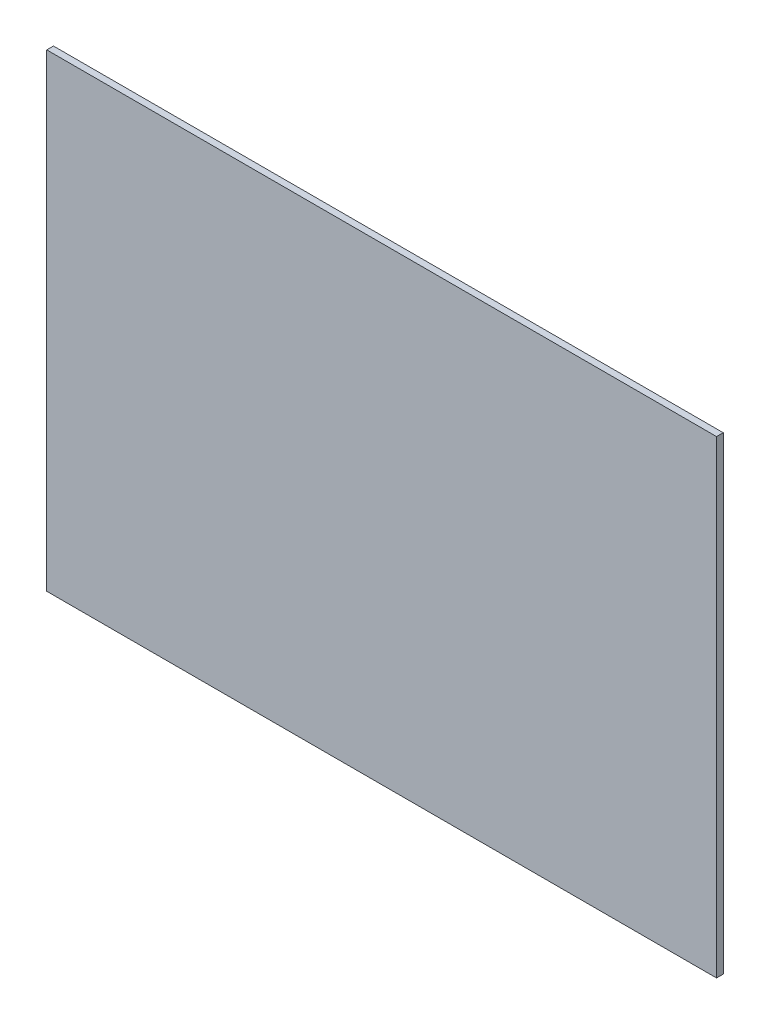
SolidWorks part; units mm, degrees
ref_plane "Alzado" through (0, 0, 0) normal (0, 0, 1) x (1, 0, 0)
ref_plane "Planta" through (0, 0, 0) normal (0, 1, 0) x (1, 0, 0)
ref_plane "Vista lateral" through (0, 0, 0) normal (1, 0, 0) x (0, 0, -1)
sketch "Croquis1" plane through (0, 0, 0) normal (0, 0, 1) x (1, 0, 0)
  line L1 (-62.4441, 24.485) -> (37.5559, 24.485)
  line L2 (-62.4441, 24.485) -> (-62.4441, -45.515)
  line L3 (-62.4441, -45.515) -> (37.5559, -45.515)
  line L4 (37.5559, 24.485) -> (37.5559, -45.515)
  dimension "D1" = 100
  dimension "D2" = 70
extrude "Saliente-Extruir1" add sketch "Croquis1" along normal blind 1
